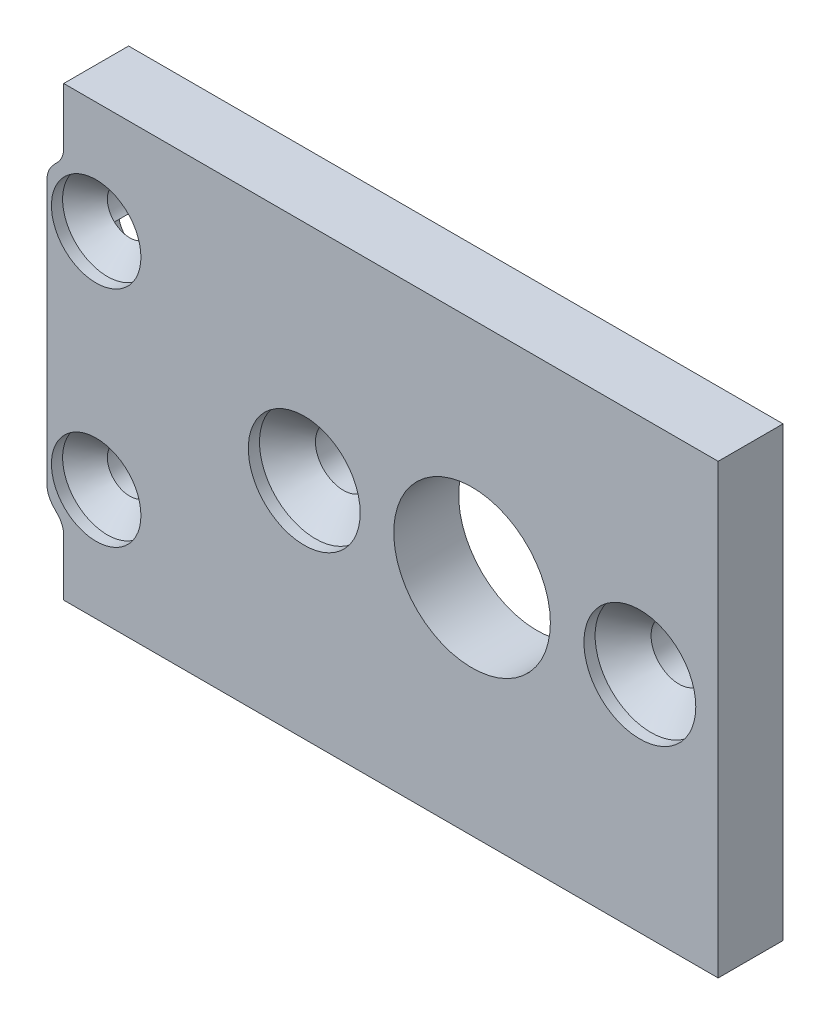
SolidWorks part; units mm, degrees
ref_plane "Front Plane" through (0, 0, 0) normal (0, 0, 1) x (1, 0, 0)
ref_plane "Top Plane" through (0, 0, 0) normal (0, 1, 0) x (1, 0, 0)
ref_plane "Right Plane" through (0, 0, 0) normal (1, 0, 0) x (0, 0, -1)
sketch "Sketch1" plane through (0, 0, 0) normal (0, 0, 1) x (1, 0, 0)
  line L1 (-92.5, 10) -> (92.5, 10)
  line L2 (-92.5, 10) -> (-92.5, -10)
  line L3 (-92.5, -10) -> (92.5, -10)
  line L4 (92.5, 10) -> (92.5, -10)
  line L5 (-92.5, 10) -> (92.5, -10) construction
  line L6 (-92.5, -10) -> (92.5, 10) construction
  point P0 (0, 0)
  dimension "D1" = 20
  dimension "D2" = 185
extrude "Base shape" add sketch "Sketch1" against normal blind 2.9
sketch "Sketch2" plane through (0, 0, 0) normal (0, 0, 1) x (1, 0, 0)
  line L0 (-83.5, 10) -> (-83.5, -10) construction
  line L1 (92.5, 10) -> (-92.5, 10) construction
  line L2 (-92.5, -10) -> (92.5, -10) construction
  line L3 (-92.5, 10) -> (-92.5, -10) construction
  line L4 (-92.5, 0) -> (92.5, 0) construction
  line L5 (92.5, -10) -> (92.5, 10) construction
  line L6 (-73.5, 10) -> (-73.5, -10) construction
  line L7 (0, 10) -> (0, -10) construction
  line L8 (73.5, 5) -> (92.5, 5) construction
  line L9 (-73.5, 3.5) -> (-92.5, 3.5) construction
  line L11 (80.5, -7) -> (66.5, -7)
  line L12 (80.5, -7) -> (80.5, 7)
  line L13 (80.5, 7) -> (66.5, 7)
  line L14 (66.5, -7) -> (66.5, 7)
  line L15 (80.5, -7) -> (66.5, 7) construction
  line L16 (80.5, 7) -> (66.5, -7) construction
  circle A0 centre (-73.5, 0) radius 10
  circle A1 centre (-81, 0) radius 1.25
  circle A2 centre (-66, 0) radius 1.25
  circle A3 centre (-73.5, 0) radius 3.5
  circle A4 centre (73.5, 0) radius 5
  circle A5 centre (66.5, 7) radius 1.25
  circle A6 centre (80.5, 7) radius 1.25
  circle A7 centre (80.5, -7) radius 1.25
  circle A8 centre (66.5, -7) radius 1.25
  dimension "D2" = 20
  dimension "D3" = 2.5
  dimension "D4" = 15
  dimension "D5" = 7
  dimension "D6" = 10
  dimension "D8" = 2.5
  dimension "D1" = 147
  dimension "D7" = 14
extrude "Motor cutouts" cut sketch "Sketch2" against normal up to next contours A5 | A6 | A7 | A8 | A1 | A2 | A3 | A4
hole_wizard "Motor M2.5 countersunks" positions "Sketch3" profile "Sketch4" countersink size "M2.5" standard "ANSI Metric" end condition through all
sketch "Sketch3" plane through (0, 0, 0) normal (0, 0, 1) x (1, 0, 0)
  point P0 (-81, 0)
  point P3 (-66, 0)
  point P7 (66.5, 7)
  point P10 (80.5, 7)
  point P13 (66.5, -7)
  point P16 (80.5, -7)
sketch "Sketch4" plane through (-81, 0, 0) normal (1, 0, 0) x (0, -1, 0)
  line L0 (0, 0) -> (0, 2.9)
  line L1 (0, 2.9) -> (1.25, 2.9)
  line L2 (1.25, 2.9) -> (1.25, 1.75)
  line L3 (1.25, 1.75) -> (2.5, 0.5)
  line L4 (2.5, 0.5) -> (2.5, 0)
  line L6 (2.5, 0) -> (0, 0)
  line L7 (-1.25, 1.75) -> (-2.5, 0.5) construction
  line L11 (0, -6.35) -> (0, 107.95) construction
  dimension "Thru Hole Dia." = 2.5
  dimension "Thru Hole Depth" = 2.9
  dimension "C'Sink Dia." = 5
  dimension "C'Sink Angle" = 90
  dimension "Head Clearance" = 0.5
sketch "Sketch5" plane through (0, 0, -2.9) normal (0, 0, -1) x (-1, 0, 0)
  line L0 (0, 10) -> (0, -10) construction
  line L3 (-92.5, 10) -> (92.5, 10) construction
  line L4 (92.5, -10) -> (-92.5, -10) construction
  line L5 (-60, -7) -> (60, -7) construction
  line L6 (-60, -6) -> (60, -6)
  line L7 (-60, -8) -> (60, -8)
  arc A0 (-60, -6) -> (-60, -8) centre (-60, -7) ccw
  arc A1 (60, -8) -> (60, -6) centre (60, -7) ccw
  point P8 (0, -7)
  dimension "D1" = 120
  dimension "D2" = 2
  dimension "D3" = 2
extrude "PCB slot" cut sketch "Sketch5" against normal blind 0.775
sketch "Sketch6" plane through (0, 0, 0) normal (0, 0, 1) x (1, 0, 0)
  line L0 (90.3, 10) -> (90.3, -10) construction
  line L1 (92.5, 10) -> (-92.5, 10) construction
  line L2 (-92.5, -10) -> (92.5, -10) construction
  line L3 (92.5, -10) -> (92.5, 10) construction
  line L4 (92.5, 0) -> (-92.5, 0) construction
  line L5 (-92.5, 10) -> (-92.5, -10) construction
  line L6 (0, 10) -> (0, -10) construction
  circle A0 centre (90.3, 5) radius 1
  circle A2 centre (90.3, -5) radius 1
  circle A3 centre (-90.3, -5) radius 1
  circle A5 centre (-90.3, 5) radius 1
  dimension "D2" = 2
  dimension "D1" = 2.2
  dimension "D3" = 10
extrude "End plate holes" cut sketch "Sketch6" against normal up to next
hole_wizard "CSK for M2 Flat Head Machine Screw3" positions "Sketch10" profile "Sketch9" countersink size "M2" standard "ANSI Metric" end condition through all
sketch "Sketch10" plane through (0, 0, 0) normal (0, 0, 1) x (1, 0, 0)
  point P2 (90.3, 5)
  point P8 (90.3, -5)
  point P11 (-90.3, 5)
  point P17 (-90.3, -5)
sketch "Sketch9" plane through (90.3, 5, 0) normal (1, 0, 0) x (0, -1, 0)
  line L0 (0, 0) -> (0, 2.9)
  line L1 (0, 2.9) -> (1, 2.9)
  line L2 (1, 2.9) -> (1, 1.5)
  line L3 (1, 1.5) -> (2, 0.5)
  line L4 (2, 0.5) -> (2, 0)
  line L6 (2, 0) -> (0, 0)
  line L7 (-1, 1.5) -> (-2, 0.5) construction
  line L11 (0, -6.35) -> (0, 107.95) construction
  dimension "Thru Hole Dia." = 2
  dimension "Thru Hole Depth" = 2.9
  dimension "C'Sink Dia." = 4
  dimension "C'Sink Angle" = 90
  dimension "Head Clearance" = 0.5
sketch "Sketch12" plane through (0, 0, -2.9) normal (0, 0, -1) x (-1, 0, 0)
  line L0 (-92.5, 0) -> (92.5, 0) construction
  line L1 (-92.5, -10) -> (-92.5, 10) construction
  line L2 (92.5, 10) -> (92.5, -10) construction
  line L3 (-90.3, 5) -> (-90.3, -5) construction
  line L4 (-88.7, 4) -> (-91.9, 0.8) construction
  line L5 (-91.9, 4) -> (-88.7, 4)
  line L6 (-91.9, 4) -> (-91.9, -4)
  line L7 (-91.9, -4) -> (-88.7, -4)
  line L8 (-88.7, 4) -> (-88.7, -4)
  line L9 (-91.9, 4) -> (-88.7, -4) construction
  line L10 (-91.9, -4) -> (-88.7, 4) construction
  line L11 (0, 10) -> (0, -10) construction
  line L12 (-92.5, 10) -> (92.5, 10) construction
  line L13 (92.5, -10) -> (-92.5, -10) construction
  line L14 (91.9, -4) -> (88.7, -4)
  line L15 (91.9, 4) -> (88.7, 4)
  line L16 (91.9, 4) -> (91.9, -4)
  line L17 (88.7, 4) -> (88.7, -4)
  circle A0 centre (-89.4071, 3.2929) radius 1
  circle A1 centre (-91.1929, 3.2929) radius 1
  circle A2 centre (-89.4071, -3.2929) radius 1
  circle A3 centre (-91.1929, -3.2929) radius 1
  circle A4 centre (89.4071, -3.2929) radius 1
  circle A5 centre (91.1929, -3.2929) radius 1
  circle A6 centre (89.4071, 3.2929) radius 1
  circle A7 centre (91.1929, 3.2929) radius 1
  point P10 (-90.3, 0)
  circle M9 centre (-90.3, -5) radius 1
  circle M10 centre (90.3, -5) radius 1
  circle M11 centre (90.3, 5) radius 1
  circle M12 centre (-90.3, 5) radius 1
  dimension "D3" = 2
  dimension "D1" = 3.2
  dimension "D2" = 8
  dimension "D4" = 45
extrude "Tap slots" cut sketch "Sketch12" against normal blind 1.4 contours A7 A6 M11 | A5 A4 M10 | A3 A2 M9 | A1 A0 M12 | A1 L5 M12 | A0 L5 M12 | A3 L7 M9 | A2 L7 M9 | A6 L15 M11 | A7 L15 M11 | A4 L14 M10 | A5 L14 M10
sketch "Sketch13" plane through (0, 0, 0) normal (0, 0, 1) x (1, 0, 0)
  line L0 (-92.5, -10) -> (92.5, -10) construction
  line L1 (-92.5, 10) -> (-91.75, 10)
  line L2 (-92.5, 10) -> (-92.5, -10)
  line L3 (-92.5, -10) -> (-91.75, -10)
  line L4 (-91.75, 10) -> (-91.75, -10)
  line L5 (-92.5, 0) -> (92.5, 0) construction
  line L6 (92.5, -10) -> (92.5, 10) construction
  line L7 (0, 10) -> (0, -10) construction
  line L8 (92.5, 10) -> (-92.5, 10) construction
  line L9 (92.5, -10) -> (91.75, -10)
  line L10 (91.75, 10) -> (91.75, -10)
  line L11 (92.5, 10) -> (91.75, 10)
  line L12 (92.5, 10) -> (92.5, -10)
  circle A0 centre (-90.3, 5) radius 2.5
  circle A1 centre (-90.3, -5) radius 2.5
  circle A2 centre (90.3, 5) radius 2.5
  circle A3 centre (90.3, -5) radius 2.5
  line M16 (92.5, -10) -> (92.5, 10)
  line M17 (92.5, 10) -> (-92.5, 10)
  line M18 (-92.5, 10) -> (-92.5, -10)
  line M19 (-92.5, -10) -> (92.5, -10)
  dimension "D2" = 5
  dimension "D1" = 0.75
extrude "Cut-Extrude3" cut sketch "Sketch13" against normal up to next contours A0 L4 M17 M18 | A1 L4 M18 M19 | L10 A2 M16 M17 | A3 L10 M16 M19
fillet "Fillet1" radius 1 8 edges at (-91.75, -7.0365, -1.45) (-92.5, -6.1874, -1.45) (-92.5, 6.1874, -1.45) (-91.75, 7.0365, -1.45) (92.5, 6.1874, -1.45) (91.75, 7.0365, -1.45) (92.5, -6.1874, -1.45) (91.75, -7.0365, -1.45)
sketch "Sketch14" plane through (0, 0, 0) normal (0, 0, 1) x (1, 0, 0)
  line L0 (-91.75, -10) -> (91.75, -10) construction
  line L1 (-62.5, -10) -> (92.5, -10)
  line L2 (-62.5, -10) -> (-62.5, 10)
  line L3 (-62.5, 10) -> (92.5, 10)
  line L4 (92.5, -10) -> (92.5, 10)
  line L5 (91.75, 10) -> (-91.75, 10) construction
  line L6 (92.5, -5.9) -> (92.5, 5.9) construction
  line L7 (-92.5, 5.9) -> (-92.5, -5.9) construction
  dimension "D1" = 30
extrude "Cut-Extrude4" cut sketch "Sketch14" against normal up to next
